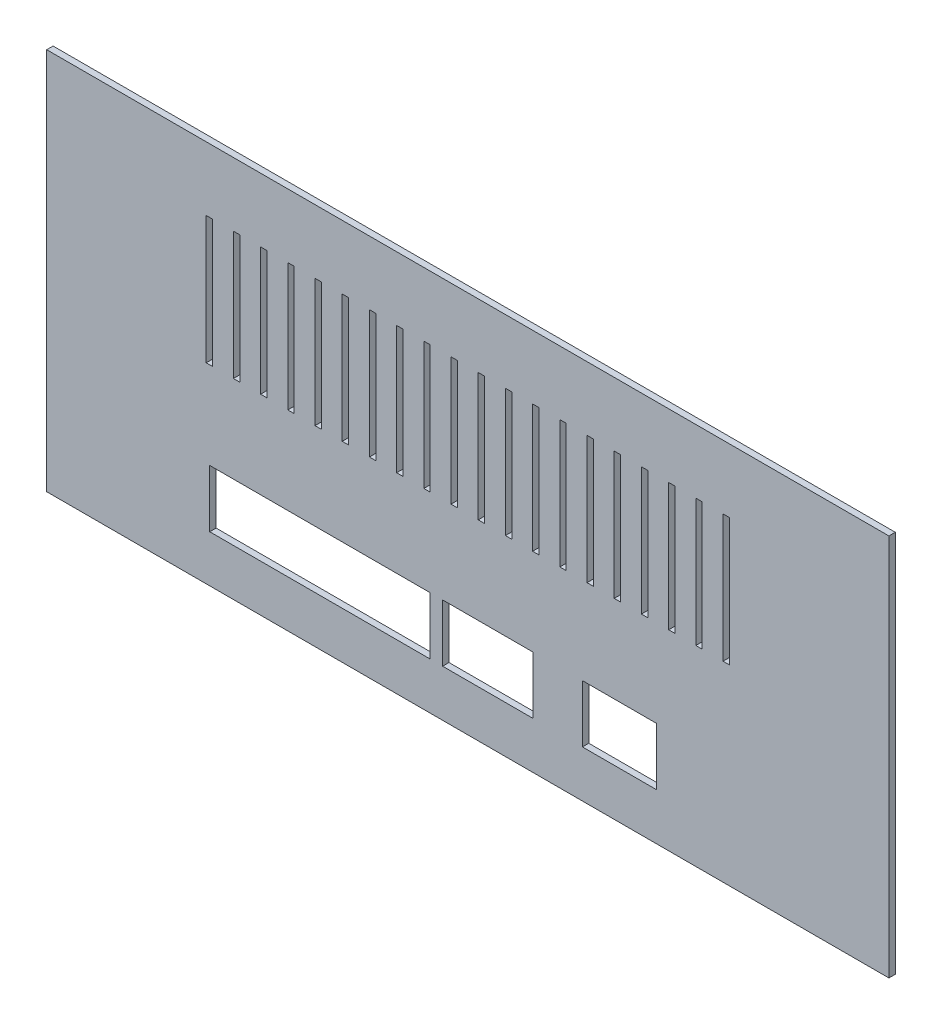
SolidWorks part; units mm, degrees
ref_plane "Front Plane" through (0, 0, 0) normal (0, 0, 1) x (1, 0, 0)
ref_plane "Top Plane" through (0, 0, 0) normal (0, 1, 0) x (1, 0, 0)
ref_plane "Right Plane" through (0, 0, 0) normal (1, 0, 0) x (0, 0, -1)
sketch "Sketch1" plane through (0, 0, 0) normal (0, 0, 1) x (1, 0, 0)
  line L1 (-48.2442, 39.6334) -> (83.7558, 39.6334)
  line L2 (-48.2442, 39.6334) -> (-48.2442, -20.3666)
  line L3 (-48.2442, -20.3666) -> (83.7558, -20.3666)
  line L4 (83.7558, 39.6334) -> (83.7558, -20.3666)
  dimension "D1" = 132
  dimension "D2" = 60
extrude "Boss-Extrude1" add sketch "Sketch1" along normal blind 1
sketch "Sketch4" plane through (0, 0, 0) normal (0, 0, -1) x (-1, 0, 0)
  line L1 (-47.3358, -13.0213) -> (-35.7158, -13.0213)
  line L2 (-47.3358, -13.0213) -> (-47.3358, -4.0213)
  line L3 (-47.3358, -4.0213) -> (-35.7158, -4.0213)
  line L4 (-35.7158, -13.0213) -> (-35.7158, -4.0213)
  line L5 (-50.8358, -11.0213) -> (-43.2158, -11.0213) construction
  line L7 (-27.9658, -13.0213) -> (-13.8058, -13.0213)
  line L8 (-83.7558, -20.3666) -> (-83.7558, 39.6334) construction
  line L9 (48.2442, -20.3666) -> (-83.7558, -20.3666) construction
  line L10 (-27.9658, -13.0213) -> (-27.9658, -4.0213)
  line L11 (-27.9658, -4.0213) -> (-13.8058, -4.0213)
  line L12 (-13.8058, -13.0213) -> (-13.8058, -4.0213)
  line L13 (-11.8058, -4.0213) -> (22.6942, -4.0213)
  line L14 (-11.8058, -4.0213) -> (-11.8058, -13.0213)
  line L15 (-11.8058, -13.0213) -> (22.6942, -13.0213)
  line L16 (22.6942, -4.0213) -> (22.6942, -13.0213)
  dimension "D1" = 7.3453
  dimension "D2" = 2
  dimension "D3" = 11.62
  dimension "D4" = 14.16
  dimension "D5" = 36.42
  dimension "D6" = 0
  dimension "D7" = 9
  dimension "D8" = 0
  dimension "D9" = 7.75
  dimension "D10" = 34.5
  dimension "D11" = 2
  dimension "D12" = 0
  dimension "D13" = 9
extrude "Cut-Extrude3" cut sketch "Sketch4" against normal through all
sketch "Sketch11" plane through (0, 0, 0) normal (0, 0, -1) x (-1, 0, 0)
  line L0 (-54.4927, 29.6334) -> (-53.4927, 29.6334)
  line L1 (-58.7558, 29.6334) -> (-57.7558, 29.6334)
  line L2 (-58.7558, 29.6334) -> (-58.7558, 9.6334)
  line L3 (-58.7558, 9.6334) -> (-57.7558, 9.6334)
  line L4 (-57.7558, 29.6334) -> (-57.7558, 9.6334)
  line L5 (-54.4927, 29.6334) -> (-54.4927, 9.6334)
  line L6 (-54.4927, 9.6334) -> (-53.4927, 9.6334)
  line L7 (-53.4927, 29.6334) -> (-53.4927, 9.6334)
  line L8 (-50.2295, 29.6334) -> (-49.2295, 29.6334)
  line L9 (-50.2295, 29.6334) -> (-50.2295, 9.6334)
  line L10 (-50.2295, 9.6334) -> (-49.2295, 9.6334)
  line L11 (-49.2295, 29.6334) -> (-49.2295, 9.6334)
  line L12 (-45.9664, 29.6334) -> (-44.9664, 29.6334)
  line L13 (-45.9664, 29.6334) -> (-45.9664, 9.6334)
  line L14 (-45.9664, 9.6334) -> (-44.9664, 9.6334)
  line L15 (-44.9664, 29.6334) -> (-44.9664, 9.6334)
  line L16 (-41.7032, 29.6334) -> (-40.7032, 29.6334)
  line L17 (-41.7032, 29.6334) -> (-41.7032, 9.6334)
  line L18 (-41.7032, 9.6334) -> (-40.7032, 9.6334)
  line L19 (-40.7032, 29.6334) -> (-40.7032, 9.6334)
  line L20 (-37.4401, 29.6334) -> (-36.4401, 29.6334)
  line L21 (-37.4401, 29.6334) -> (-37.4401, 9.6334)
  line L22 (-37.4401, 9.6334) -> (-36.4401, 9.6334)
  line L23 (-36.4401, 29.6334) -> (-36.4401, 9.6334)
  line L24 (-33.1769, 29.6334) -> (-32.1769, 29.6334)
  line L25 (-33.1769, 29.6334) -> (-33.1769, 9.6334)
  line L26 (-33.1769, 9.6334) -> (-32.1769, 9.6334)
  line L27 (-32.1769, 29.6334) -> (-32.1769, 9.6334)
  line L28 (-28.9137, 29.6334) -> (-27.9137, 29.6334)
  line L29 (-28.9137, 29.6334) -> (-28.9137, 9.6334)
  line L30 (-28.9137, 9.6334) -> (-27.9137, 9.6334)
  line L31 (-27.9137, 29.6334) -> (-27.9137, 9.6334)
  line L32 (-24.6506, 29.6334) -> (-23.6506, 29.6334)
  line L33 (-24.6506, 29.6334) -> (-24.6506, 9.6334)
  line L34 (-24.6506, 9.6334) -> (-23.6506, 9.6334)
  line L35 (-23.6506, 29.6334) -> (-23.6506, 9.6334)
  line L36 (-20.3874, 29.6334) -> (-19.3874, 29.6334)
  line L37 (-20.3874, 29.6334) -> (-20.3874, 9.6334)
  line L38 (-20.3874, 9.6334) -> (-19.3874, 9.6334)
  line L39 (-19.3874, 29.6334) -> (-19.3874, 9.6334)
  line L40 (-16.1243, 29.6334) -> (-15.1243, 29.6334)
  line L41 (-16.1243, 29.6334) -> (-16.1243, 9.6334)
  line L42 (-16.1243, 9.6334) -> (-15.1243, 9.6334)
  line L43 (-15.1243, 29.6334) -> (-15.1243, 9.6334)
  line L44 (-11.8611, 29.6334) -> (-10.8611, 29.6334)
  line L45 (-11.8611, 29.6334) -> (-11.8611, 9.6334)
  line L46 (-11.8611, 9.6334) -> (-10.8611, 9.6334)
  line L47 (-10.8611, 29.6334) -> (-10.8611, 9.6334)
  line L48 (-7.598, 29.6334) -> (-6.598, 29.6334)
  line L49 (-7.598, 29.6334) -> (-7.598, 9.6334)
  line L50 (-7.598, 9.6334) -> (-6.598, 9.6334)
  line L51 (-6.598, 29.6334) -> (-6.598, 9.6334)
  line L52 (-3.3348, 29.6334) -> (-2.3348, 29.6334)
  line L53 (-3.3348, 29.6334) -> (-3.3348, 9.6334)
  line L54 (-3.3348, 9.6334) -> (-2.3348, 9.6334)
  line L55 (-2.3348, 29.6334) -> (-2.3348, 9.6334)
  line L56 (0.9284, 29.6334) -> (1.9284, 29.6334)
  line L57 (0.9284, 29.6334) -> (0.9284, 9.6334)
  line L58 (0.9284, 9.6334) -> (1.9284, 9.6334)
  line L59 (1.9284, 29.6334) -> (1.9284, 9.6334)
  line L60 (5.1915, 29.6334) -> (6.1915, 29.6334)
  line L61 (5.1915, 29.6334) -> (5.1915, 9.6334)
  line L62 (5.1915, 9.6334) -> (6.1915, 9.6334)
  line L63 (6.1915, 29.6334) -> (6.1915, 9.6334)
  line L64 (9.4547, 29.6334) -> (10.4547, 29.6334)
  line L65 (9.4547, 29.6334) -> (9.4547, 9.6334)
  line L66 (9.4547, 9.6334) -> (10.4547, 9.6334)
  line L67 (10.4547, 29.6334) -> (10.4547, 9.6334)
  line L68 (13.7178, 29.6334) -> (14.7178, 29.6334)
  line L69 (13.7178, 29.6334) -> (13.7178, 9.6334)
  line L70 (13.7178, 9.6334) -> (14.7178, 9.6334)
  line L71 (14.7178, 29.6334) -> (14.7178, 9.6334)
  line L72 (17.981, 29.6334) -> (18.981, 29.6334)
  line L73 (17.981, 29.6334) -> (17.981, 9.6334)
  line L74 (17.981, 9.6334) -> (18.981, 9.6334)
  line L75 (18.981, 29.6334) -> (18.981, 9.6334)
  line L76 (22.2442, 29.6334) -> (23.2442, 29.6334)
  line L77 (22.2442, 29.6334) -> (22.2442, 9.6334)
  line L78 (22.2442, 9.6334) -> (23.2442, 9.6334)
  line L79 (23.2442, 29.6334) -> (23.2442, 9.6334)
  line L80 (-83.7558, -20.3666) -> (-83.7558, 39.6334) construction
  line L81 (48.2442, 39.6334) -> (48.2442, -20.3666) construction
  line L82 (-83.7558, 39.6334) -> (48.2442, 39.6334) construction
  dimension "D1" = 1
  dimension "D2" = 20
  dimension "D4" = 25
  dimension "D5" = 25
  dimension "D6" = 10
  dimension "D3" = 20
extrude "Cut-Extrude6" cut sketch "Sketch11" against normal through all
